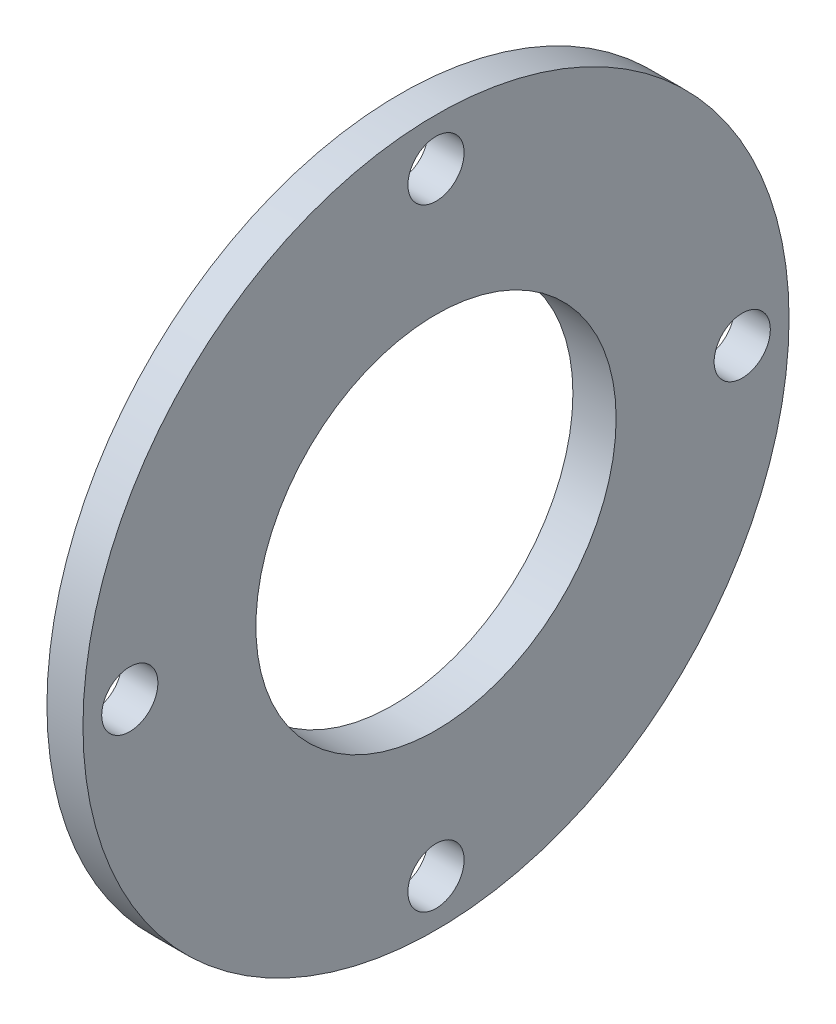
SolidWorks part; units mm, degrees
ref_plane "Front Plane" through (0, 0, 0) normal (0, 0, 1) x (1, 0, 0)
ref_plane "Top Plane" through (0, 0, 0) normal (0, 1, 0) x (1, 0, 0)
ref_plane "Right Plane" through (0, 0, 0) normal (1, 0, 0) x (0, 0, -1)
sketch "Sketch1" plane through (0, 0, 0) normal (0, 0, 1) x (1, 0, 0)
  line L0 (0, 31) -> (0, 36)
  line L1 (0, -55) -> (0, 55) construction
  line L2 (0, 36) -> (3, 36)
  line L3 (3, 36) -> (3, 49)
  line L4 (3, 49) -> (8, 49)
  line L5 (8, 49) -> (8, 25)
  line L6 (8, 25) -> (2, 25)
  line L7 (2, 25) -> (2, 31)
  line L8 (2, 31) -> (0, 31)
  line L9 (55, 0) -> (-55, 0) construction
  line L10 (0, 0) -> (-47.7721, 0) construction
  dimension "D1" = 6
  dimension "D2" = 2
  dimension "D3" = 25
  dimension "D4" = 5
  dimension "D5" = 36
  dimension "D6" = 13
  dimension "D7" = 5
revolve "Revolve1" add sketch "Sketch1" angle 360 about L10
sketch "Sketch3" plane through (3, 0, 0) normal (-1, 0, 0) x (0, 0, 1)
  circle A0 centre (0, 0) radius 42.5
  circle A1 centre (42.5, 0) radius 3.9
  dimension "D1" = 85
  dimension "D2" = 7.8
extrude "Cut-Extrude1" cut sketch "Sketch3" against normal blind 10 contours A1
pattern_circular "CirPattern1" count 4 over 360 about axis through (0, 0, 0) along (1, 0, 0) of "Cut-Extrude1"
